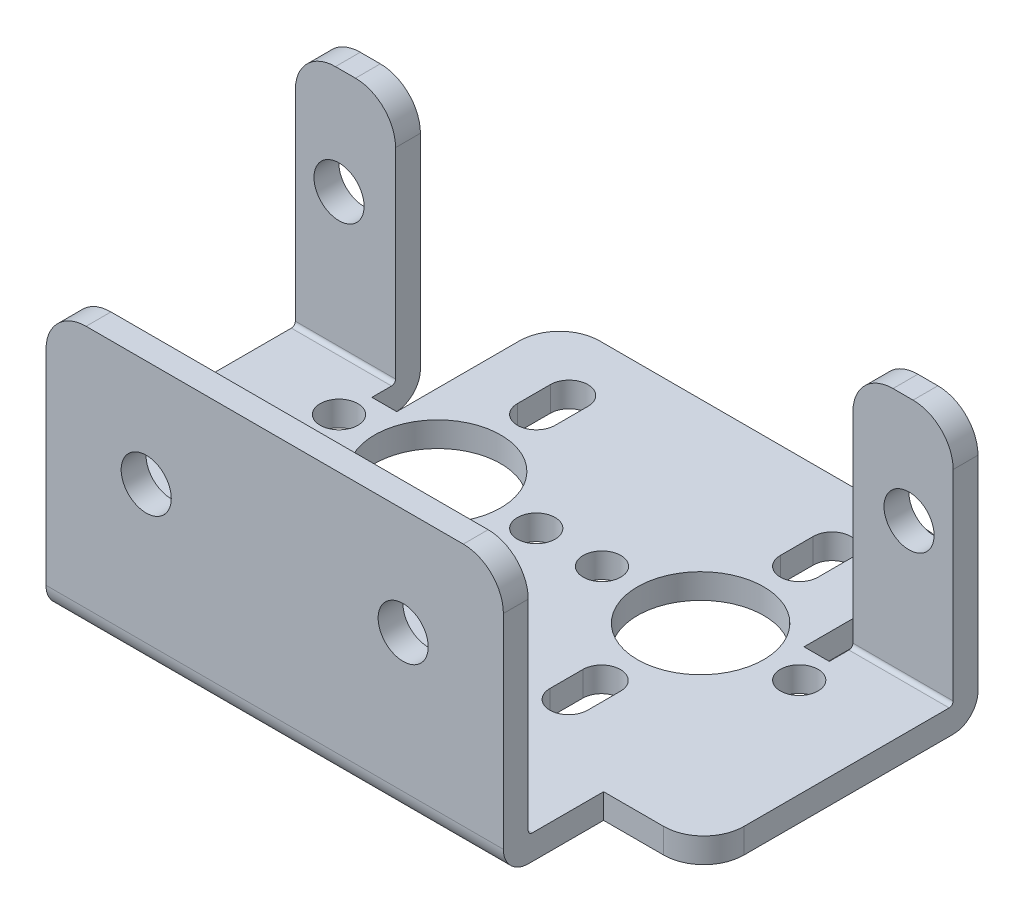
SolidWorks part; units mm, degrees
ref_plane "Front Plane" through (0, 0, 0) normal (0, 0, 1) x (1, 0, 0)
ref_plane "Top Plane" through (0, 0, 0) normal (0, 1, 0) x (1, 0, 0)
ref_plane "Right Plane" through (0, 0, 0) normal (1, 0, 0) x (0, 0, -1)
sketch "Sketch1" plane through (0, 0, 0) normal (1, 0, 0) x (0, 0, -1)
  line L1 (0, 0) -> (30.9626, 0)
  line L2 (0, 0) -> (0, 17.0688)
  line L3 (0, 17.0688) -> (30.9626, 17.0688)
  line L4 (30.9626, 0) -> (30.9626, 17.0688)
  dimension "D1" = 17.0688
  dimension "D2" = 30.9626
extrude "Extrude1" add sketch "Sketch1" along normal blind 41.6814
sketch "Sketch3" plane through (41.6814, 0, 0) normal (1, 0, 0) x (0, 0, -1)
  line L0 (0, 17.0688) -> (0, 0)
  line L1 (0, 0) -> (30.9626, 0)
  line L2 (30.9626, 0) -> (30.9626, 1.5748)
  line L3 (30.9626, 0) -> (30.9626, 17.0688) construction
  line L4 (30.9626, 1.5748) -> (23.7236, 1.5748)
  line L5 (23.7236, 1.5748) -> (23.7236, 17.0688)
  line L6 (30.9626, 17.0688) -> (0, 17.0688) construction
  line L7 (23.7236, 17.0688) -> (22.1488, 17.0688)
  line L8 (22.1488, 17.0688) -> (22.1488, 1.5748)
  line L9 (22.1488, 1.5748) -> (1.5748, 1.5748)
  line L10 (1.5748, 1.5748) -> (1.5748, 17.0688)
  line L11 (1.5748, 17.0688) -> (0, 17.0688)
  dimension "D1" = 1.5748
  dimension "D2" = 1.5748
  dimension "D3" = 1.5748
  dimension "D4" = 23.7236
extrude "Extrude2" cut sketch "Sketch3" against normal through all flip side to cut
sketch "Sketch4" plane through (0, 0, 0) normal (0, 0, 1) x (1, 0, 0)
  line L0 (41.6814, 0) -> (0, 0) construction
  line L1 (0, 17.0688) -> (6.35, 17.0688)
  line L2 (0, 17.0688) -> (0, 0)
  line L3 (0, 0) -> (6.35, 0)
  line L4 (6.35, 17.0688) -> (6.35, 0)
  line L6 (35.3314, 0) -> (41.6814, 0)
  line L7 (35.3314, 0) -> (35.3314, 17.0688)
  line L8 (35.3314, 17.0688) -> (41.6814, 17.0688)
  line L9 (41.6814, 0) -> (41.6814, 17.0688)
  dimension "D1" = 6.35
  dimension "D2" = 6.35
extrude "Extrude3" cut sketch "Sketch4" against normal blind 6.35
sketch "Sketch5" plane through (0, 1.5748, 0) normal (0, 1, 0) x (1, 0, 0)
  line L0 (0, 23.7236) -> (41.6814, 23.7236) construction
  line L1 (0, 30.9626) -> (6.35, 30.9626)
  line L2 (0, 30.9626) -> (0, 23.7236)
  line L3 (0, 23.7236) -> (6.35, 23.7236)
  line L4 (6.35, 30.9626) -> (6.35, 23.7236)
  line L6 (41.6814, 30.9626) -> (35.3314, 30.9626)
  line L7 (41.6814, 30.9626) -> (41.6814, 23.7236)
  line L8 (41.6814, 23.7236) -> (35.3314, 23.7236)
  line L9 (35.3314, 30.9626) -> (35.3314, 23.7236)
  dimension "D1" = 6.35
  dimension "D2" = 6.35
extrude "Extrude4" cut sketch "Sketch5" against normal up to surface (1.5748 mm away) up to face at (20.8407, 0, -10.9157)
sketch "Sketch6" plane through (0, 0, -23.7236) normal (0, 0, -1) x (-1, 0, 0)
  line L1 (-35.3314, 1.5748) -> (-6.35, 1.5748)
  line L2 (-35.3314, 1.5748) -> (-35.3314, 17.0688)
  line L3 (-35.3314, 17.0688) -> (-6.35, 17.0688)
  line L4 (-6.35, 1.5748) -> (-6.35, 17.0688)
extrude "Extrude5" cut sketch "Sketch6" against normal up to surface (1.5748 mm away) up to face at (20.8407, 9.3218, -22.1488)
sketch "Sketch7" plane through (0, 0, -30.9626) normal (0, 0, -1) x (-1, 0, 0)
  line L0 (-35.3314, 0) -> (-6.35, 0) construction
  line L1 (-35.3314, 1.5748) -> (-33.7312, 1.5748)
  line L2 (-35.3314, 1.5748) -> (-35.3314, 0)
  line L3 (-35.3314, 0) -> (-33.7312, 0)
  line L4 (-33.7312, 1.5748) -> (-33.7312, 0)
  line L5 (-41.6814, 0) -> (-41.6814, 17.0688) construction
  line L6 (-6.35, 1.5748) -> (-7.9248, 1.5748)
  line L7 (-6.35, 1.5748) -> (-6.35, 0)
  line L8 (-6.35, 0) -> (-7.9248, 0)
  line L9 (-7.9248, 1.5748) -> (-7.9248, 0)
  dimension "D1" = 7.9502
  dimension "D2" = 33.7566
extrude "Extrude6" cut sketch "Sketch7" against normal blind 10.3124
fillet "Fillet1" radius 1.5875 3 edges at (20.8407, 0, 0) (3.175, 0, -23.7236) (38.5064, 0, -23.7236)
fillet "Fillet2" radius 0.254 3 edges at (20.8407, 1.5748, -1.5748) (38.5064, 1.5748, -22.1488) (3.175, 1.5748, -22.1488)
sketch "Sketch8" plane through (0, 1.5748, 0) normal (0, 1, 0) x (1, 0, 0)
  line L0 (0, 21.8948) -> (0, 6.35) construction
  line L1 (35.3314, 0) -> (6.35, 0) construction
  line L2 (13.6906, 27.0002) -> (13.6906, 24.9174)
  line L3 (11.303, 27.0002) -> (11.303, 24.9174)
  line L4 (13.6906, 12.3952) -> (13.6906, 10.3124)
  line L5 (11.303, 12.3952) -> (11.303, 10.3124)
  line L6 (27.9654, 12.3952) -> (27.9654, 10.3124)
  line L7 (27.9654, 27.0002) -> (27.9654, 24.9174)
  line L8 (30.353, 27.0002) -> (30.353, 24.9174)
  line L9 (30.353, 12.3952) -> (30.353, 10.3124)
  circle A0 centre (12.4968, 18.669) radius 4.0005
  circle A1 centre (12.4968, 18.669) radius 6.2484 construction
  circle A2 centre (18.7452, 18.669) radius 1.1938
  circle A3 centre (6.2484, 18.669) radius 1.1938
  arc A4 (11.303, 24.9174) -> (13.6906, 24.9174) centre (12.4968, 24.9174) ccw
  arc A5 (13.6906, 27.0002) -> (11.303, 27.0002) centre (12.4968, 27.0002) ccw
  arc A6 (13.6906, 12.3952) -> (11.303, 12.3952) centre (12.4968, 12.3952) ccw
  arc A7 (11.303, 10.3124) -> (13.6906, 10.3124) centre (12.4968, 10.3124) ccw
  arc A8 (27.9654, 10.3124) -> (30.353, 10.3124) centre (29.1592, 10.3124) ccw
  circle A9 centre (22.9108, 18.669) radius 1.1938
  circle A10 centre (29.1592, 18.669) radius 4.0005
  arc A11 (30.353, 12.3952) -> (27.9654, 12.3952) centre (29.1592, 12.3952) ccw
  arc A12 (27.9654, 24.9174) -> (30.353, 24.9174) centre (29.1592, 24.9174) ccw
  arc A13 (30.353, 27.0002) -> (27.9654, 27.0002) centre (29.1592, 27.0002) ccw
  circle A14 centre (35.4076, 18.669) radius 1.1938
  dimension "D1" = 12.4968
  dimension "D3" = 18.7452
  dimension "D4" = 2.3876
  dimension "D6" = 2.3876
  dimension "D10" = 2.3876
  dimension "D11" = 2.3876
  dimension "D2" = 18.669
  dimension "D5" = 24.9174
  dimension "D7" = 27.0002
  dimension "D8" = 12.3952
  dimension "D9" = 10.3124
extrude "Extrude7" cut sketch "Sketch8" against normal up to surface (1.5748 mm away) up to face at (20.8375, 0, -16.3528)
sketch "Sketch9" plane through (0, 0, 0) normal (0, 0, 1) x (1, 0, 0)
  line L0 (0, 0) -> (6.35, 0) construction
  line L2 (0, 17.0688) -> (0, 1.8288) construction
  circle A0 centre (2.7686, 10.3124) radius 1.5875
  circle A1 centre (12.7, 10.3124) radius 1.5875
  circle A2 centre (28.9814, 10.3124) radius 1.5875
  circle A3 centre (38.8874, 10.3124) radius 1.5875
  dimension "D1" = 3.175
  dimension "D2" = 3.175
  dimension "D3" = 3.175
  dimension "D4" = 3.175
  dimension "D5" = 10.3124
  dimension "D6" = 2.7686
  dimension "D7" = 12.7
  dimension "D8" = 28.9814
  dimension "D9" = 38.8874
extrude "Extrude9" cut sketch "Sketch9" against normal through all
fillet "Fillet3" radius 2.54 10 edges at (0, 0.7874, -6.35) (41.6814, 0.7874, -6.35) (6.35, 17.0688, -0.7874) (35.3314, 17.0688, -0.7874) (35.3314, 17.0688, -22.9362) (0, 17.0688, -22.9362) (6.35, 17.0688, -22.9362) (41.6814, 17.0688, -22.9362) (7.9248, 0.7874, -30.9626) (33.7312, 0.7874, -30.9626)
